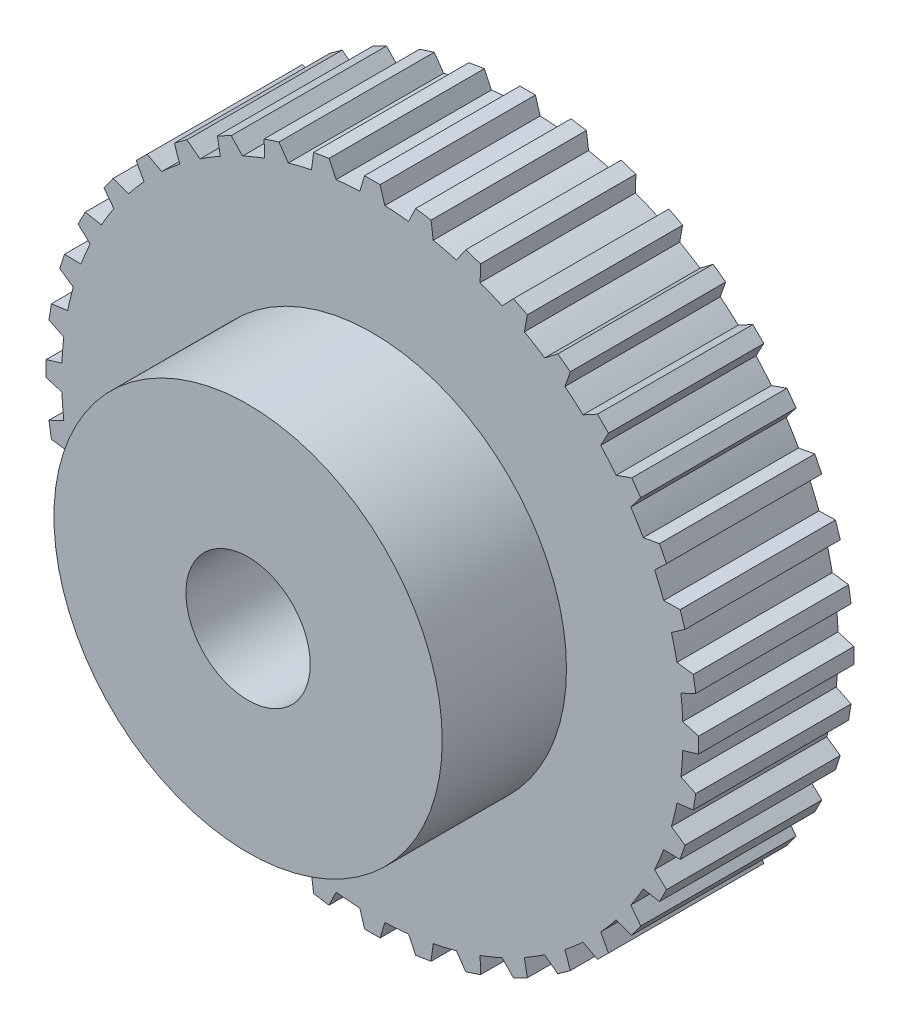
SolidWorks part; units mm, degrees
material "AISI 1045 鋼，冷拉"
ref_plane "前基準面" through (0, 0, 0) normal (0, 0, 1) x (1, 0, 0)
ref_plane "上基準面" through (0, 0, 0) normal (0, 1, 0) x (1, 0, 0)
ref_plane "右基準面" through (0, 0, 0) normal (1, 0, 0) x (0, 0, -1)
sketch "草圖1" plane through (0, 0, 0) normal (0, 0, 1) x (1, 0, 0)
  circle A0 centre (0, 0) radius 20
  dimension "D1" = 40
extrude "填料-伸長1" add sketch "草圖1" along normal blind 10
sketch "草圖2" plane through (0, 0, 10) normal (0, 0, 1) x (1, 0, 0)
  circle A0 centre (0, 0) radius 12.5
  dimension "D1" = 25
extrude "填料-伸長2" add sketch "草圖2" along normal blind 8
sketch "草圖3" plane through (0, 0, 18) normal (0, 0, 1) x (1, 0, 0)
  circle A0 centre (0, 0) radius 4
  dimension "D1" = 8
extrude "除料-伸長1" cut sketch "草圖3" against normal through all
sketch "草圖4" plane through (0, 0, 0) normal (0, 0, -1) x (-1, 0, 0)
  line L0 (0, 20) -> (0, 0) construction
  line L1 (-0.5, 21) -> (0.5, 21)
  line L2 (0.5, 21) -> (2, 16)
  line L3 (2, 16) -> (-2, 16)
  line L4 (-2, 16) -> (-0.5, 21)
  circle A0 centre (0, 0) radius 20 construction
  point P8 (0, 21)
  dimension "D1" = 1
  dimension "D2" = 4
  dimension "D3" = 5
  dimension "D4" = 21
extrude "填料-伸長3" add sketch "草圖4" against normal blind 10
pattern_circular "環狀複製排列1" count 40 over 360 about axis through (0, 0, 0) along (0, 0, 1) of "填料-伸長3"
